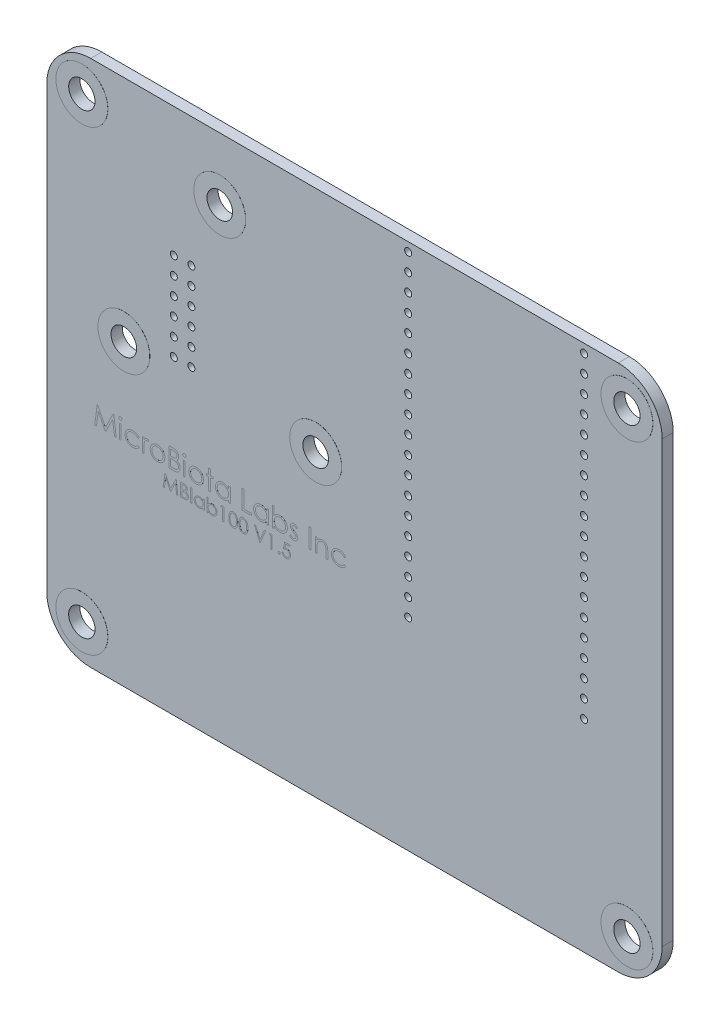
SolidWorks part; units mm, degrees
ref_plane "Front Plane" through (0, 0, 0) normal (0, 0, 1) x (1, 0, 0)
ref_plane "Top Plane" through (0, 0, 0) normal (0, 1, 0) x (1, 0, 0)
ref_plane "Right Plane" through (0, 0, 0) normal (1, 0, 0) x (0, 0, -1)
sketch "Sketch1" plane through (0, 0, 0) normal (0, 0, 1) x (1, 0, 0)
  line L1 (0, -76.2) -> (88.9, -76.2)
  line L2 (0, -76.2) -> (0, 0)
  line L3 (0, 0) -> (88.9, 0)
  line L4 (88.9, -76.2) -> (88.9, 0)
  dimension "D1" = 76.2
  dimension "D2" = 88.9
extrude "Boss-Extrude1" add sketch "Sketch1" along normal blind 1.6
sketch "Sketch2" plane through (0, 0, 0) normal (0, 0, -1) x (-1, 0, 0)
  circle A8 centre (-11.1436, -33) radius 1.85 construction
  circle A9 centre (-38.8564, -33) radius 1.85 construction
  circle A10 centre (-25, -9) radius 1.85 construction
  circle A11 centre (-11.1436, -33) radius 1.85
  circle A12 centre (-38.8564, -33) radius 1.85
  circle A13 centre (-25, -9) radius 1.85
extrude "Cut-Extrude1" cut sketch "Sketch2" against normal through all
sketch "Sketch4" plane through (0, 0, 0) normal (0, 0, -1) x (-1, 0, 0)
  line L0 (-44.45, 0) -> (-44.45, -76.2) construction
  line L1 (-88.9, 0) -> (0, 0) construction
  line L2 (0, -76.2) -> (-88.9, -76.2) construction
  line L3 (-88.9, -38.1) -> (0, -38.1) construction
  line L4 (-88.9, -76.2) -> (-88.9, 0) construction
  line L5 (0, 0) -> (0, -76.2) construction
  circle A0 centre (-5.08, -5.08) radius 1.905
  circle A1 centre (-83.82, -5.08) radius 1.905
  circle A2 centre (-83.82, -71.12) radius 1.905
  circle A3 centre (-5.08, -71.12) radius 1.905
  dimension "D1" = 3.81
  dimension "D2" = 5.08
  dimension "D3" = 5.08
extrude "Cut-Extrude2" cut sketch "Sketch4" against normal through all
fillet "Fillet1" radius 6.35 4 edges at (88.9, 0, 0.8) (88.9, -76.2, 0.8) (0, -76.2, 0.8) (0, 0, 0.8)
ref_plane "Plane1" through (44.45, 0, 0) normal (-1, 0, 0) x (0, 0, 1)
sketch "Sketch6" plane through (0, 0, 0) normal (0, 0, -1) x (-1, 0, 0)
  circle A0 centre (-5.08, -71.12) radius 3.75
  circle A1 centre (-5.08, -5.08) radius 3.75
  circle A2 centre (-38.8564, -33) radius 3.75
  circle A3 centre (-11.1436, -33) radius 3.75
  circle A4 centre (-25, -9) radius 3.75
  circle A5 centre (-83.82, -5.08) radius 3.75
  circle A6 centre (-83.82, -71.12) radius 3.75
  circle M3 centre (-5.08, -71.12) radius 1.905
  circle M4 centre (-83.82, -71.12) radius 1.905
  circle M5 centre (-83.82, -5.08) radius 1.905
  circle M6 centre (-5.08, -5.08) radius 1.905
  circle M7 centre (-11.1436, -33) radius 1.85
  circle M8 centre (-38.8564, -33) radius 1.85
  circle M9 centre (-25, -9) radius 1.85
  dimension "D1" = 7.5
extrude "Boss-Extrude2" add sketch "Sketch6" along normal blind 0.01 contours A1 M6 | A4 M9 | A2 M8 | A0 M3 | A3 M7 | A5 M5 | A6 M4
ref_plane "Plane2" through (0, 0, 0.8) normal (0, 0, 1) x (1, 0, 0)
mirror "Mirror1" about plane through (0, 0, 0.8) normal (0, 0, 1) of "Boss-Extrude2"
sketch "Sketch7" plane through (0, 0, 1.6) normal (0, 0, 1) x (1, 0, 0)
  line L4 (52.41, -1.0821) -> (52.01, -1.0821)
  line L5 (52.01, -1.0821) -> (52.01, -1.4821)
  line L6 (52.01, -1.4821) -> (52.41, -1.4821)
  line L7 (52.41, -1.4821) -> (52.41, -1.0821)
  line L8 (52.41, -1.0821) -> (52.01, -1.0821)
  line L11 (52.41, -1.4821) -> (52.41, -1.0821)
  circle A0 centre (20.893, -31.35) radius 0.508
  circle A1 centre (18.353, -31.35) radius 0.508
  circle A2 centre (18.353, -28.81) radius 0.508
  circle A3 centre (18.353, -26.27) radius 0.508
  circle A4 centre (18.353, -23.73) radius 0.508
  circle A5 centre (18.353, -21.19) radius 0.508
  circle A6 centre (18.353, -18.65) radius 0.508
  circle A7 centre (20.893, -28.81) radius 0.508
  circle A8 centre (20.893, -26.27) radius 0.508
  circle A9 centre (20.893, -23.73) radius 0.508
  circle A10 centre (20.893, -21.19) radius 0.508
  circle A11 centre (20.893, -18.65) radius 0.508
  circle A12 centre (52.21, -1.2821) radius 0.508
  circle A13 centre (77.61, -1.2821) radius 0.508
  circle A14 centre (77.61, -3.8221) radius 0.508
  circle A15 centre (77.61, -6.3621) radius 0.508
  circle A16 centre (77.61, -8.9021) radius 0.508
  circle A17 centre (77.61, -11.4421) radius 0.508
  circle A18 centre (77.61, -13.9821) radius 0.508
  circle A19 centre (77.61, -16.5221) radius 0.508
  circle A20 centre (77.61, -19.0621) radius 0.508
  circle A21 centre (77.61, -21.6021) radius 0.508
  circle A22 centre (77.61, -24.1421) radius 0.508
  circle A23 centre (77.61, -26.6821) radius 0.508
  circle A24 centre (77.61, -29.2221) radius 0.508
  circle A25 centre (77.61, -31.7621) radius 0.508
  circle A26 centre (77.61, -34.3021) radius 0.508
  circle A27 centre (77.61, -36.8421) radius 0.508
  circle A28 centre (77.61, -39.3821) radius 0.508
  circle A29 centre (77.61, -41.9221) radius 0.508
  circle A30 centre (77.61, -44.4621) radius 0.508
  circle A31 centre (77.61, -47.0021) radius 0.508
  circle A32 centre (52.21, -3.8221) radius 0.508
  circle A33 centre (52.21, -6.3621) radius 0.508
  circle A34 centre (52.21, -8.9021) radius 0.508
  circle A35 centre (52.21, -11.4421) radius 0.508
  circle A36 centre (52.21, -13.9821) radius 0.508
  circle A37 centre (52.21, -16.5221) radius 0.508
  circle A38 centre (52.21, -19.0621) radius 0.508
  circle A39 centre (52.21, -21.6021) radius 0.508
  circle A40 centre (52.21, -24.1421) radius 0.508
  circle A41 centre (52.21, -26.6821) radius 0.508
  circle A42 centre (52.21, -29.2221) radius 0.508
  circle A43 centre (52.21, -31.7621) radius 0.508
  circle A44 centre (52.21, -34.3021) radius 0.508
  circle A45 centre (52.21, -36.8421) radius 0.508
  circle A46 centre (52.21, -39.3821) radius 0.508
  circle A47 centre (52.21, -41.9221) radius 0.508
  circle A48 centre (52.21, -44.4621) radius 0.508
  circle A49 centre (52.21, -47.0021) radius 0.508
  point P0 (20.893, -31.35)
  point P6 (52.21, -1.2821)
  point P30 (52.41, -1.2821)
  point P32 (52.21, -1.0821)
  point P33 (77.4242, -1.4821)
  point P34 (17.3159, -19.8613)
  point P35 (17.6903, -18.7039)
  point P112 (20.103, -31.35)
  dimension "D1" = 6
  dimension "D4" = 19
  dimension "D5" = 25.4
  dimension "D6" = 12.7
  dimension "D7" = 2.54
  dimension "D3" = 0
  dimension "D2" = 2
extrude "Cut-Extrude3" cut sketch "Sketch7" against normal through all contours A0 | A1 | A2 | A7 | A3 | A8 | A4 | A9 | A11 | A6 | A10 | A5 | A31 | A30 | A29 | A28 | A27 | A26 | A25 | A24 | A23 | A22 | A21 | A20 | A19 | A18 | A17 | A16 | A15 | A14 | A13 | A34 | A35 | A36 | A37 | A38 | A39 | A40 | A41 | A42 | A43 | A12 | A32 | A33 | A44 | A45 | A46 | A47 | A48 | A49
sketch "Sketch5" plane through (0, 0, 1.6) normal (0, 0, 1) x (1, 0, 0)
  line L0 (0, -6.35) -> (0, -69.85) construction
  line L1 (6.35, -76.2) -> (82.55, -76.2) construction
  line L2 (82.55, 0) -> (6.35, 0) construction
  line L3 (0, -6.35) -> (0, -69.85) construction
  line L4 (82.55, 0) -> (6.35, 0) construction
  circle A0 centre (5.08, -71.12) radius 1.905 construction
  circle A3 centre (5.08, -71.12) radius 1.905
  circle A5 centre (38.8564, -33) radius 1.85 construction
  circle A7 centre (15.8595, 55.8131) radius 3 construction
  circle A10 centre (11.1436, -33) radius 1.85 construction
  point P0 (5.08, -5.08)
  point P1 (5.08, -71.12)
  point P3 (83.82, -71.12)
  point P5 (83.82, -5.08)
  point P7 (25, -9)
  point P9 (18.353, -18.65)
  point P15 (0, -76.2)
  point P17 (11.1436, -33)
  point P30 (0, 0)
  point P31 (52.21, -1.2821)
  point P32 (38.8564, -33)
  dimension "D9" = 33
  dimension "D10" = 3.81
  dimension "D2" = 5.08
  dimension "D3" = 9
  dimension "D4" = 25
  dimension "D5" = 71.12
  dimension "D6" = 38.8564
  dimension "D7" = 11.1436
  dimension "D8" = 83.82
  dimension "D12" = 18.353
  dimension "D13" = 52.21
  dimension "D14" = 55.8131
  dimension "D15" = 18.65
  dimension "D16" = 18.65
  dimension "D11" = 5.08
sketch "Sketch8" plane through (0, 0, 1.6) normal (0, 0, 1) x (1, 0, 0)
  line L0 (6.7093, -45.5936) -> (48.8367, -45.5936) construction
  line L1 (16.6754, -48.3901) -> (40.7088, -48.3901) construction
  text T0 "MicroBiota Labs Inc" font "Century Gothic" height 2.794
  text T1 "MBlab100 V1.5" font "Century Gothic" height 1.905
  point P5 (6.7093, -45.5936)
extrude "Boss-Extrude3" add sketch "Sketch8" along normal blind 0.001
